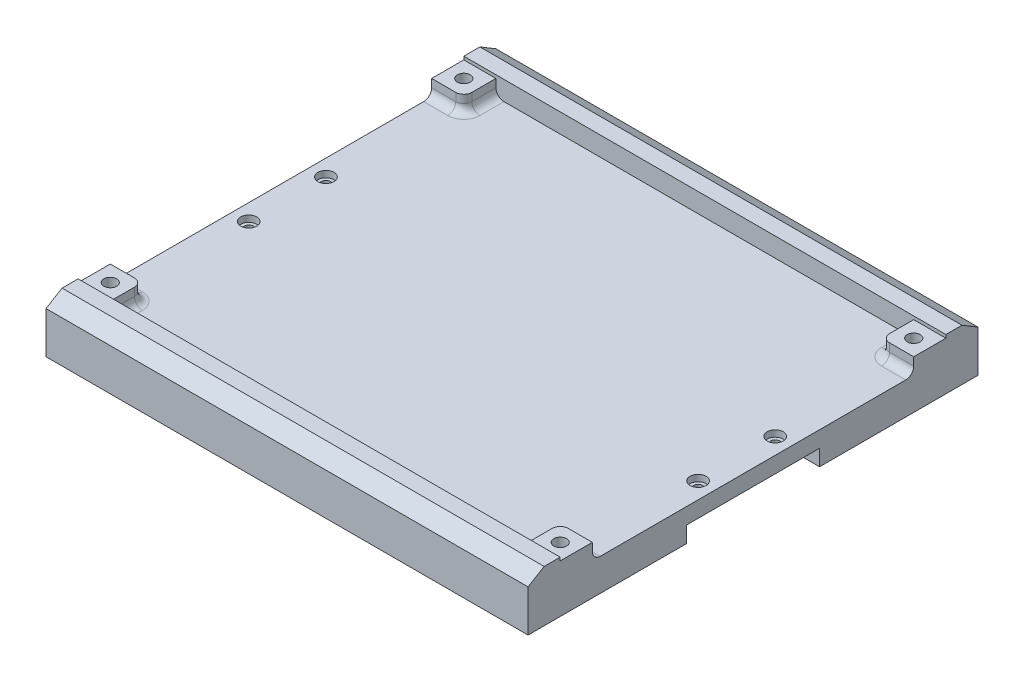
SolidWorks part; units mm, degrees
ref_plane "Front Plane" through (0, 0, 0) normal (0, 0, 1) x (1, 0, 0)
ref_plane "Top Plane" through (0, 0, 0) normal (0, 1, 0) x (1, 0, 0)
ref_plane "Right Plane" through (0, 0, 0) normal (1, 0, 0) x (0, 0, -1)
sketch "Sketch1" plane through (0, 0, 0) normal (0, 1, 0) x (1, 0, 0)
  line L1 (-75, 70) -> (75, 70)
  line L2 (-75, 70) -> (-75, -70)
  line L3 (-75, -70) -> (75, -70)
  line L4 (75, 70) -> (75, -70)
  line L5 (-75, 70) -> (75, -70) construction
  line L6 (-75, -70) -> (75, 70) construction
  point P0 (0, 0)
  dimension "D1" = 150
  dimension "D2" = 140
extrude "Boss-Extrude1" add sketch "Sketch1" along normal blind 10
sketch "Sketch2" plane through (0, 0, 0) normal (0, -1, 0) x (1, 0, 0)
  line L0 (-75, 0) -> (75, 0) construction
  line L1 (-75, -70) -> (-75, 70) construction
  line L2 (75, 70) -> (75, -70) construction
  line L3 (0, 70) -> (0, -70) construction
  line L4 (-75.1, 20.7) -> (-64.7, 20.7)
  line L5 (-75.1, 20.7) -> (-75.1, -20.7)
  line L6 (-75.1, -20.7) -> (-64.7, -20.7)
  line L7 (-64.7, 20.7) -> (-64.7, -20.7)
  line L8 (-75.1, 20.7) -> (-64.7, -20.7) construction
  line L9 (-75.1, -20.7) -> (-64.7, 20.7) construction
  line L10 (-75, 70) -> (75, 70) construction
  line L11 (75, -70) -> (-75, -70) construction
  line L12 (75.1, -20.7) -> (64.7, 20.7) construction
  line L13 (75.1, 20.7) -> (64.7, -20.7) construction
  line L14 (64.7, 20.7) -> (64.7, -20.7)
  line L15 (75.1, -20.7) -> (64.7, -20.7)
  line L16 (75.1, 20.7) -> (75.1, -20.7)
  line L17 (75.1, 20.7) -> (64.7, 20.7)
  point P6 (-69.9, 0)
  point P21 (69.9, 0)
  dimension "D1" = 41.4
  dimension "D2" = 10.4
  dimension "D3" = 5.1
extrude "Cut-Extrude1" cut sketch "Sketch2" against normal blind 5
sketch "Sketch3" plane through (-75, 0, 0) normal (-1, 0, 0) x (0, 0, 1)
  line L0 (0, 10) -> (0, 0) construction
  line L7 (-70, 10) -> (-60, 10)
  line L8 (-70, 10) -> (-70, 16)
  line L9 (-70, 16) -> (-60, 16)
  line L10 (-60, 10) -> (-60, 16)
  line L11 (-70, 10) -> (70, 10) construction
  line L16 (-70, 13) -> (-65, 16)
  line L17 (70, 13) -> (65, 16)
  line L22 (60, 10) -> (60, 16)
  line L23 (70, 16) -> (60, 16)
  line L24 (70, 10) -> (70, 16)
  line L25 (70, 10) -> (60, 10)
  dimension "D1" = 10
  dimension "D2" = 6
extrude "Boss-Extrude2" add sketch "Sketch3" against normal blind 150
sketch "Sketch4" plane through (0, 10, 0) normal (0, 1, 0) x (1, 0, 0)
  line L0 (0, 60) -> (0, 50) construction
  line L5 (-75, 60) -> (75, 60)
  line L6 (-75, 60) -> (-75, 50)
  line L7 (-75, 50) -> (75, 50)
  line L8 (75, 60) -> (75, 50)
  line L9 (-75, 0) -> (75, 0) construction
  line L10 (-75, 60) -> (-75, -60) construction
  line L11 (75, -60) -> (75, 60) construction
  line L12 (-75, 60) -> (-75, 50)
  line L13 (75, 60) -> (75, 50)
  line L14 (-75, 60) -> (-75, 50)
  line L15 (75, 60) -> (75, 50)
  line L16 (-75, 60) -> (-75, 50)
  line L17 (75, 60) -> (75, 50)
  line L18 (0, -60) -> (0, -50) construction
  line L19 (75, -60) -> (75, -50)
  line L20 (-75, -60) -> (-75, -50)
  line L21 (75, -60) -> (75, -50)
  line L22 (-75, -60) -> (-75, -50)
  line L23 (75, -60) -> (75, -50)
  line L24 (-75, -60) -> (-75, -50)
  line L25 (75, -60) -> (75, -50)
  line L26 (-75, -50) -> (75, -50)
  line L27 (-75, -60) -> (-75, -50)
  line L28 (-75, -60) -> (75, -60)
  circle A4 centre (-70, 55) radius 2
  circle A5 centre (70, 55) radius 2
  circle A6 centre (-70, 55) radius 2
  circle A7 centre (70, 55) radius 2
  circle A8 centre (-70, 55) radius 2
  circle A9 centre (70, 55) radius 2
  circle A10 centre (-70, 55) radius 2
  circle A11 centre (70, 55) radius 2
  circle A12 centre (70, -55) radius 2
  circle A13 centre (-70, -55) radius 2
  circle A14 centre (70, -55) radius 2
  circle A15 centre (-70, -55) radius 2
  circle A16 centre (70, -55) radius 2
  circle A17 centre (-70, -55) radius 2
  circle A18 centre (70, -55) radius 2
  circle A19 centre (-70, -55) radius 2
  dimension "D3" = 5
  dimension "D5" = 4
  dimension "D1" = 10
  dimension "D2" = 150
  dimension "D4" = 5
extrude "Boss-Extrude3" add sketch "Sketch4" along normal blind 5
sketch "Sketch5" plane through (0, 15, 0) normal (0, 1, 0) x (1, 0, 0)
  circle A0 centre (-70, 55) radius 2
  circle A1 centre (70, 55) radius 2
  circle A2 centre (-70, -55) radius 2
  circle A3 centre (70, -55) radius 2
extrude "Cut-Extrude2" cut sketch "Sketch5" against normal blind 6
sketch "Sketch6" plane through (0, 5, 0) normal (0, -1, 0) x (-1, 0, 0)
  line L0 (75, 0) -> (64.7, 0) construction
  line L1 (75, -20.7) -> (75, 20.7) construction
  line L2 (64.7, 20.7) -> (64.7, -20.7) construction
  line L3 (0, -70) -> (0, 70) construction
  line L4 (75, -70) -> (-75, -70) construction
  line L5 (-75, 70) -> (75, 70) construction
  circle A0 centre (69.9, -11.9999) radius 1.5
  circle A1 centre (69.9, 11.9999) radius 1.5
  circle A2 centre (69.9, -11.9999) radius 1.5
  circle A3 centre (69.9, 11.9999) radius 1.5
  circle A4 centre (-69.9, 11.9999) radius 1.5
  circle A5 centre (-69.9, 11.9999) radius 1.5
  circle A6 centre (-69.9, -11.9999) radius 1.5
  circle A7 centre (-69.9, -11.9999) radius 1.5
  point P14 (69.85, 0)
  dimension "D2" = 3
  dimension "D1" = 12
extrude "Cut-Extrude3" cut sketch "Sketch6" against normal blind 5 contours A0 | A1 | A6 | A4
sketch "Sketch7" plane through (0, 10, 0) normal (0, 1, 0) x (1, 0, 0)
  line L0 (0, 50) -> (0, -50) construction
  line L1 (-75, 50) -> (75, 50) construction
  line L2 (-75, -50) -> (75, -50) construction
  circle A0 centre (-69.9, 11.9999) radius 2.5
  circle A1 centre (-69.9, -11.9999) radius 2.5
  circle A2 centre (69.9, -11.9999) radius 2.5
  circle A3 centre (69.9, 11.9999) radius 2.5
  dimension "D1" = 5
  dimension "D2" = 5
extrude "Cut-Extrude4" cut sketch "Sketch7" against normal blind 2
sketch "Sketch8" plane through (0, 15, 0) normal (0, 1, 0) x (1, 0, 0)
  line L0 (0, 60) -> (0, -60) construction
  line L1 (75, 60) -> (-75, 60) construction
  line L2 (-75, -60) -> (75, -60) construction
  line L3 (75, -60) -> (-75, -60) construction
  line L4 (-65, 60) -> (65, 60)
  line L5 (-65, 60) -> (-65, -60)
  line L6 (-65, -60) -> (65, -60)
  line L7 (65, 60) -> (65, -60)
  line L8 (-65, 60) -> (65, -60) construction
  line L9 (-65, -60) -> (65, 60) construction
  point P6 (0, 0)
  dimension "D1" = 130
extrude "Cut-Extrude5" cut sketch "Sketch8" against normal blind 5
fillet "Fillet1" radius 2.5 12 edges at (65, 12.5, 50) (70, 10, 50) (65, 10, 55) (-65, 10, 55) (-70, 10, 50) (-65, 12.5, 50) (65, 12.5, -50) (-65, 12.5, -50) (65, 10, -55) (70, 10, -50) (-65, 10, -55) (-70, 10, -50)
